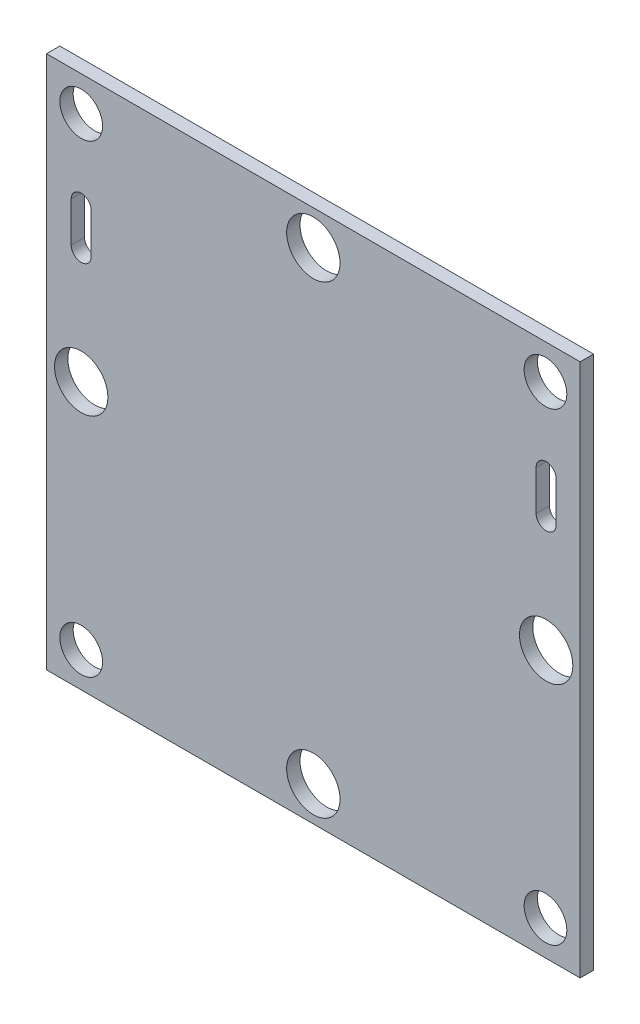
SolidWorks part; units mm, degrees
ref_plane "Front Plane" through (0, 0, 0) normal (0, 0, 1) x (1, 0, 0)
ref_plane "Top Plane" through (0, 0, 0) normal (0, 1, 0) x (1, 0, 0)
ref_plane "Right Plane" through (0, 0, 0) normal (1, 0, 0) x (0, 0, -1)
sketch "Sketch1" plane through (0, 0, 0) normal (0, 0, 1) x (1, 0, 0)
  line L1 (-20, 20) -> (20, 20)
  line L2 (-20, 20) -> (-20, -20)
  line L3 (-20, -20) -> (20, -20)
  line L4 (20, 20) -> (20, -20)
  line L5 (-20, 20) -> (20, -20) construction
  line L6 (-20, -20) -> (20, 20) construction
  point P0 (0, 0)
  dimension "D1" = 40
  dimension "D2" = 40
extrude "Boss-Extrude1" add sketch "Sketch1" along normal blind 1
sketch "Sketch2" plane through (0, 0, 1) normal (0, 0, 1) x (1, 0, 0)
  line L0 (-20, 20) -> (-20, -20) construction
  line L1 (20, 20) -> (-20, 20) construction
  line L2 (20, -20) -> (20, 20) construction
  line L3 (-20, -20) -> (20, -20) construction
  line L4 (-17.4, 11.5) -> (-17.4, 8.5) construction
  line L5 (-16.65, 11.5) -> (-16.65, 8.5)
  line L6 (-18.15, 11.5) -> (-18.15, 8.5)
  line L7 (17.4507, 11.5) -> (17.4507, 8.5) construction
  line L8 (18.2007, 11.5) -> (18.2007, 8.5)
  line L9 (16.7007, 11.5) -> (16.7007, 8.5)
  circle A0 centre (-17.4, -17.4) radius 1.6
  circle A1 centre (17.4, -17.4) radius 1.6
  circle A2 centre (17.4, 17.4) radius 1.6
  circle A3 centre (-17.4, 17.4) radius 1.6
  circle A4 centre (0, 17.4) radius 2
  circle A5 centre (17.4507, 0) radius 2
  circle A6 centre (0, -17.4) radius 2
  circle A7 centre (-17.4, 0) radius 2
  arc A8 (-16.65, 11.5) -> (-18.15, 11.5) centre (-17.4, 11.5) ccw
  arc A9 (-18.15, 8.5) -> (-16.65, 8.5) centre (-17.4, 8.5) ccw
  arc A10 (18.2007, 11.5) -> (16.7007, 11.5) centre (17.4507, 11.5) ccw
  arc A11 (16.7007, 8.5) -> (18.2007, 8.5) centre (17.4507, 8.5) ccw
  point P26 (-17.4, 10)
  point P33 (17.4507, 10)
  dimension "D1" = 2.6
  dimension "D5" = 10
  dimension "D6" = 20
  dimension "D2" = 2.6
  dimension "D3" = 2.6
  dimension "D4" = 2.6
  dimension "D7" = 20
extrude "Cut-Extrude1" cut sketch "Sketch2" against normal blind 10
